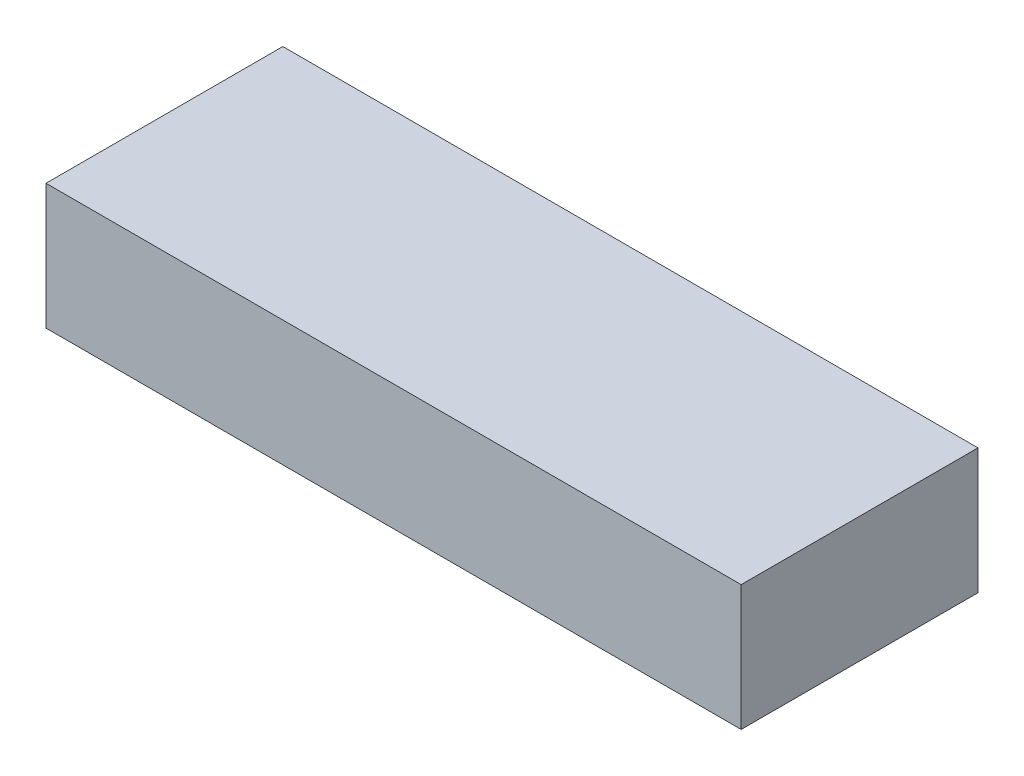
SolidWorks part; units mm, degrees
ref_plane "Front Plane" through (0, 0, 0) normal (0, 0, 1) x (1, 0, 0)
ref_plane "Top Plane" through (0, 0, 0) normal (0, 1, 0) x (1, 0, 0)
ref_plane "Right Plane" through (0, 0, 0) normal (1, 0, 0) x (0, 0, -1)
sketch "Sketch1" plane through (0, 0, 0) normal (0, 1, 0) x (1, 0, 0)
  line L1 (-68.961, 23.495) -> (68.961, 23.495)
  line L2 (-68.961, 23.495) -> (-68.961, -23.495)
  line L3 (-68.961, -23.495) -> (68.961, -23.495)
  line L4 (68.961, 23.495) -> (68.961, -23.495)
  line L5 (-68.961, 23.495) -> (68.961, -23.495) construction
  line L6 (-68.961, -23.495) -> (68.961, 23.495) construction
  point P0 (0, 0)
  dimension "D1" = 137.922
  dimension "D2" = 46.99
extrude "Boss-Extrude1" add sketch "Sketch1" along normal blind 24.892
